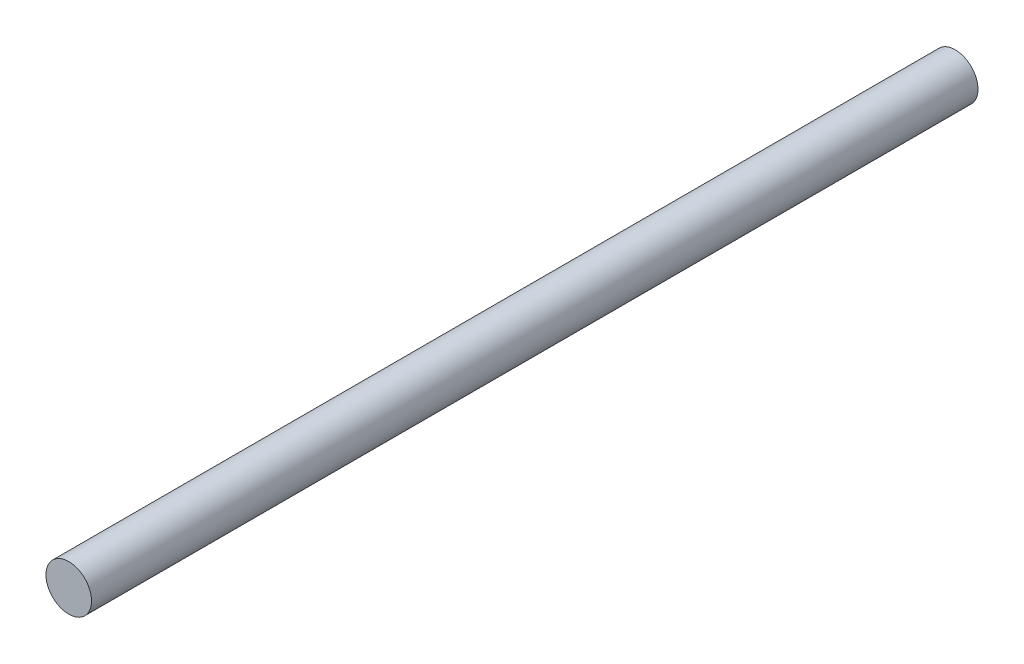
SolidWorks part; units mm, degrees
ref_plane "Front Plane" through (0, 0, 0) normal (0, 0, 1) x (1, 0, 0)
ref_plane "Top Plane" through (0, 0, 0) normal (0, 1, 0) x (1, 0, 0)
ref_plane "Right Plane" through (0, 0, 0) normal (1, 0, 0) x (0, 0, -1)
sketch "Sketch1" plane through (0, 0, 0) normal (0, 0, 1) x (1, 0, 0)
  circle A0 centre (0, 0) radius 14.5034
extrude "Boss-Extrude1" add sketch "Sketch1" along normal blind 563.88
